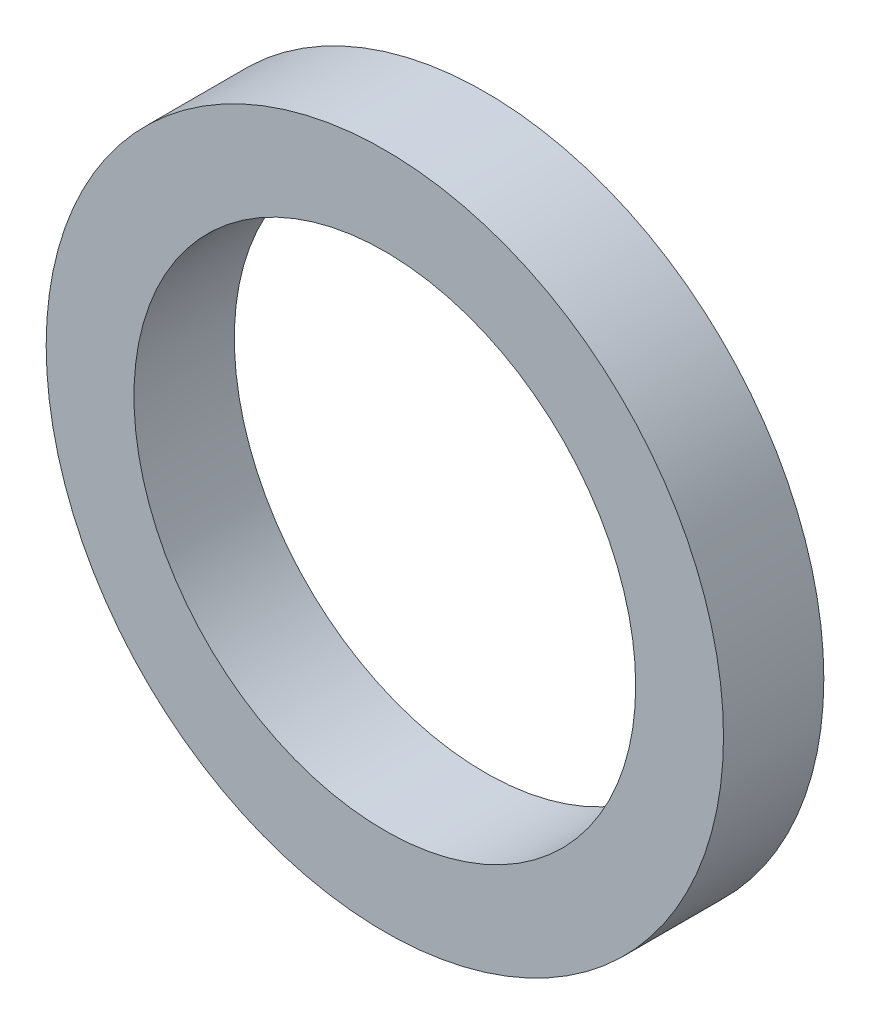
SolidWorks part; units mm, degrees
ref_plane "前视基准面" through (0, 0, 0) normal (0, 0, 1) x (1, 0, 0)
ref_plane "上视基准面" through (0, 0, 0) normal (0, 1, 0) x (1, 0, 0)
ref_plane "右视基准面" through (0, 0, 0) normal (1, 0, 0) x (0, 0, -1)
sketch "草图1" plane through (0, 0, 0) normal (0, 0, 1) x (1, 0, 0)
  circle A0 centre (0, 0) radius 10
  circle A1 centre (0, 0) radius 13.5
extrude "凸台-拉伸1" add sketch "草图1" along normal blind 4
